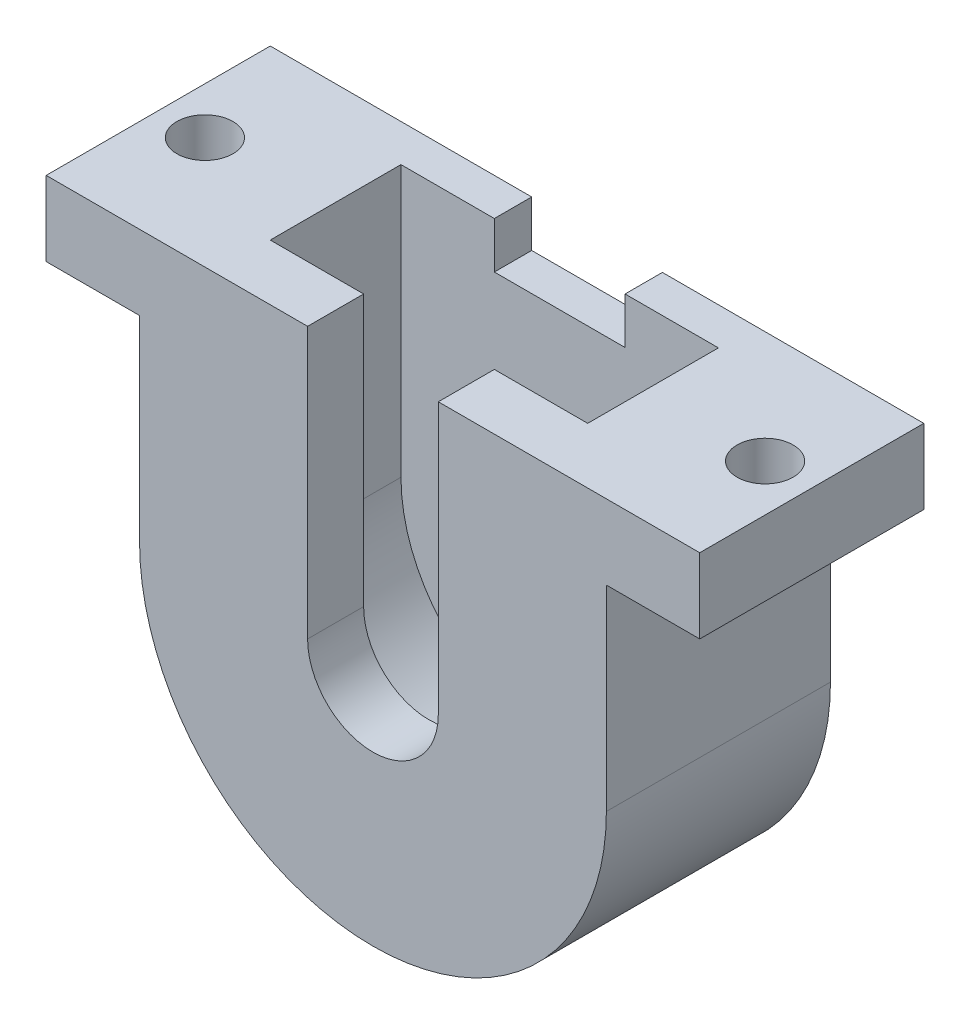
SolidWorks part; units mm, degrees
ref_plane "Alzado" through (0, 0, 0) normal (0, 0, 1) x (1, 0, 0)
ref_plane "Planta" through (0, 0, 0) normal (0, 1, 0) x (1, 0, 0)
ref_plane "Vista lateral" through (0, 0, 0) normal (1, 0, 0) x (0, 0, -1)
sketch "Croquis1" plane through (0, 0, 0) normal (0, 0, 1) x (1, 0, 0)
  line L1 (10.5, 10.5) -> (12.5, 10.5)
  line L2 (-10.5, 10.5) -> (-12.5, 10.5)
  line L4 (12.5, 10.5) -> (12.5, 0)
  line L5 (-12.5, 0) -> (-12.5, 10.5)
  line L6 (8.5, 0) -> (8.5, 10.5)
  line L7 (8.5, 10.5) -> (10.5, 10.5)
  line L8 (-8.5, 0) -> (-8.5, 10.5)
  line L9 (-8.5, 10.5) -> (-10.5, 10.5)
  arc A1 (-12.5, 0) -> (12.5, 0) centre (0, 0) ccw
  arc A2 (-8.5, 0) -> (8.5, 0) centre (0, 0) ccw
  dimension "D3" = 17
extrude "Saliente-Extruir1" add sketch "Croquis1" along normal blind 38
sketch "Croquis2" plane through (0, 0, 38) normal (0, 0, 1) x (1, 0, 0)
  line L0 (-12.5, 10.5) -> (-3.5, 10.5)
  line L1 (-3.5, 10.5) -> (-3.5, 0)
  line L2 (3.5, 0) -> (3.5, 10.5)
  line L3 (3.5, 10.5) -> (12.5, 10.5)
  line L4 (-12.5, 10.5) -> (-12.5, 0)
  line L5 (12.5, 10.5) -> (12.5, 0)
  arc A0 (-3.5, 0) -> (3.5, 0) centre (0, 0) ccw
  arc A1 (-12.5, 0) -> (12.5, 0) centre (0, 0) ccw
  dimension "D1" = 7
extrude "Saliente-Extruir2" add sketch "Croquis2" along normal blind 3
sketch "Croquis3" plane through (0, 0, 0) normal (0, 0, -1) x (-1, 0, 0)
  line L0 (-12.5, 10.5) -> (12.5, 10.5)
  line L1 (12.5, 10.5) -> (12.5, 0)
  line L2 (-12.5, 10.5) -> (-12.5, 0)
  arc A0 (-12.5, 0) -> (12.5, 0) centre (0, 0) ccw
extrude "Saliente-Extruir3" add sketch "Croquis3" along normal blind 2
sketch "Croquis4" plane through (0, 10.5, 0) normal (0, 1, 0) x (1, 0, 0)
  line L1 (17.5, -41) -> (3.5, -41)
  line L2 (-17.5, -41) -> (-17.5, -26.5656)
  line L3 (17.5, -26.5656) -> (17.5, -41)
  line L4 (17.5, -26.5656) -> (8.5, -26.5656)
  line L5 (-8.5, -38) -> (-8.5, -26.5656)
  line L7 (8.5, -38) -> (8.5, -26.5656)
  line L9 (-8.5, -38) -> (-3.5, -38)
  line L10 (-3.5, -38) -> (-3.5, -41)
  line L14 (8.5, -38) -> (3.5, -38)
  line L15 (3.5, -38) -> (3.5, -41)
  line L16 (-3.5, -41) -> (-17.5, -41)
  line L17 (-8.5, -26.5656) -> (-17.5, -26.5656)
  circle A2 centre (15, -35) radius 1.5
  circle A3 centre (-15, -35) radius 1.5
extrude "Saliente-Extruir4" add sketch "Croquis4" along normal blind 4
sketch "Croquis5" plane through (0, 10.5, 0) normal (0, -1, 0) x (1, 0, 0)
  line L0 (17.5, 41) -> (17.5, 26.5656) construction
  line L1 (-17.5, -2) -> (17.5, -2)
  line L2 (-17.5, -2) -> (-17.5, 29)
  line L3 (-17.5, 29) -> (17.5, 29)
  line L4 (17.5, -2) -> (17.5, 29)
  line L6 (-17.5, 41) -> (-12.5, 41) construction
  dimension "D1" = 12
extrude "Cortar-Extruir1" cut sketch "Croquis5" against normal through all and the other way through all
sketch "Croquis6" plane through (0, 0, 29) normal (0, 0, -1) x (-1, 0, 0)
  line L0 (-8.5, 14.5) -> (-3.5, 14.5)
  line L1 (-3.5, 14.5) -> (-3.5, 12.0175)
  line L2 (-3.5, 14.5) -> (-3.5, 0) construction
  line L3 (-3.5, 12.0175) -> (3.5, 12.0175)
  line L4 (3.5, 0) -> (3.5, 14.5) construction
  line L5 (3.5, 12.0175) -> (3.5, 14.5)
  line L6 (3.5, 14.5) -> (8.5, 14.5)
  line L7 (8.5, 14.5) -> (8.5, 0)
  line L8 (-8.5, 14.5) -> (-8.5, 0)
  arc A0 (-8.5, 0) -> (8.5, 0) centre (0, 0) ccw
extrude "Saliente-Extruir5" add sketch "Croquis6" against normal blind 2
